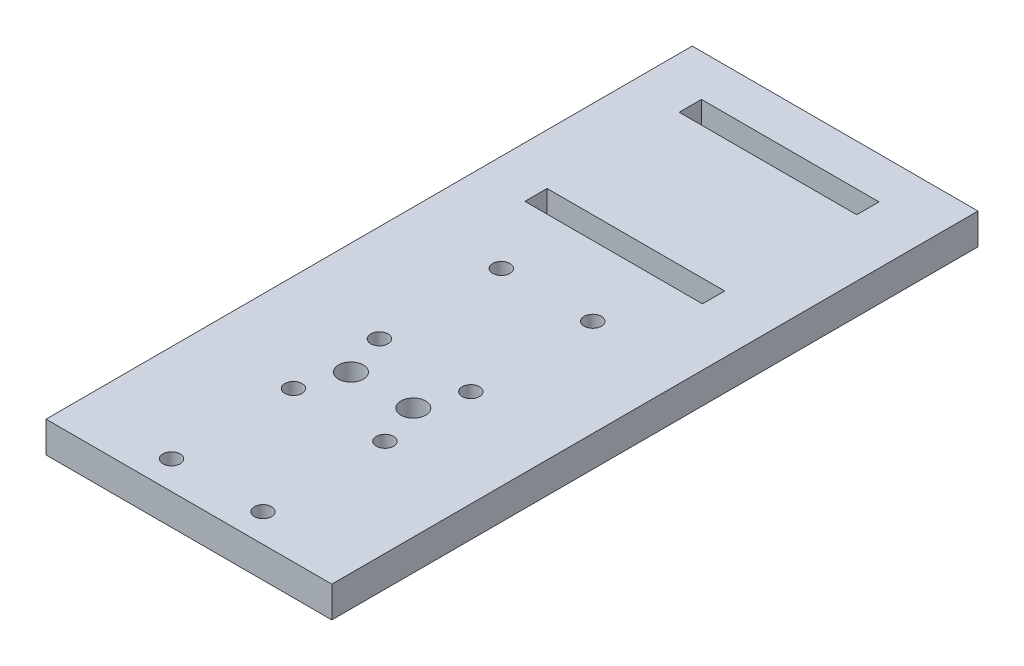
SolidWorks part; units mm, degrees
ref_plane "Front Plane" through (0, 0, 0) normal (0, 0, 1) x (1, 0, 0)
ref_plane "Top Plane" through (0, 0, 0) normal (0, 1, 0) x (1, 0, 0)
ref_plane "Right Plane" through (0, 0, 0) normal (1, 0, 0) x (0, 0, -1)
sketch "Sketch1" plane through (0, 0, 0) normal (0, 1, 0) x (1, 0, 0)
  line L0 (27.5, 74.38) -> (27.5, 0) construction
  line L1 (0, 0) -> (55, 0)
  line L2 (0, 0) -> (0, 74.38)
  line L3 (0, 74.38) -> (55, 74.38)
  line L4 (55, 0) -> (55, 74.38)
  line L5 (0, 37.19) -> (55, 37.19) construction
  circle A0 centre (18.7, 68.92) radius 1.66
  circle A1 centre (36.3, 68.92) radius 1.66
  circle A2 centre (36.3, 45.46) radius 1.66
  circle A3 centre (18.7, 45.46) radius 1.66
  circle A4 centre (18.7, 28.92) radius 1.66
  circle A5 centre (36.3, 28.92) radius 1.66
  circle A6 centre (36.3, 5.46) radius 1.66
  circle A7 centre (18.7, 5.46) radius 1.66
  circle A9 centre (21.5, 37.19) radius 2.3813
  circle A10 centre (33.5, 37.19) radius 2.3813
  dimension "D4" = 3.32
  dimension "D7" = 4.7625
  dimension "D1" = 74.38
  dimension "D2" = 55
  dimension "D3" = 23.46
  dimension "D5" = 17.6
  dimension "D6" = 5.46
  dimension "D8" = 6
extrude "Boss-Extrude1" add sketch "Sketch1" along normal blind 5.969
sketch "Sketch2" plane through (0, 5.969, 0) normal (0, 1, 0) x (1, 0, 0)
  line L1 (55, 74.38) -> (0, 74.38)
  line L2 (55, 74.38) -> (55, 124.36)
  line L3 (55, 124.36) -> (0, 124.36)
  line L4 (0, 74.38) -> (0, 124.36)
  line L5 (55, 99.37) -> (0, 99.37) construction
  line L6 (43.95, 112.08) -> (9.78, 116.36) construction
  line L7 (43.95, 82.38) -> (9.78, 82.38)
  line L8 (43.95, 82.38) -> (43.95, 86.66)
  line L9 (43.95, 86.66) -> (9.78, 86.66)
  line L10 (9.78, 82.38) -> (9.78, 86.66)
  line L11 (43.95, 82.38) -> (9.78, 86.66) construction
  line L12 (43.95, 86.66) -> (9.78, 82.38) construction
  line L13 (43.95, 116.36) -> (9.78, 112.08) construction
  line L14 (9.78, 116.36) -> (9.78, 112.08)
  line L15 (43.95, 112.08) -> (9.78, 112.08)
  line L16 (43.95, 116.36) -> (43.95, 112.08)
  line L17 (43.95, 116.36) -> (9.78, 116.36)
  point P12 (26.865, 84.52)
  point P18 (26.865, 114.22)
  dimension "D1" = 49.98
  dimension "D2" = 8
  dimension "D3" = 4.28
  dimension "D4" = 9.78
  dimension "D5" = 34.17
extrude "Boss-Extrude2" add sketch "Sketch2" against normal blind 5.969
